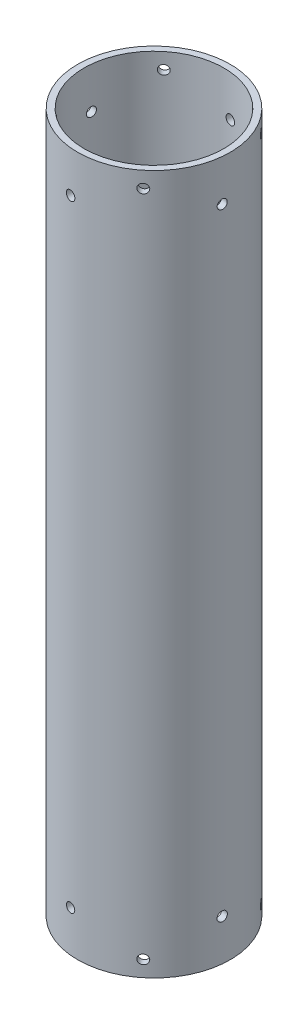
SolidWorks part; units mm, degrees
material "Thornel Mat VMA"
ref_plane "前视基准面" through (0, 0, 0) normal (0, 0, 1) x (1, 0, 0)
ref_plane "上视基准面" through (0, 0, 0) normal (0, 1, 0) x (1, 0, 0)
ref_plane "右视基准面" through (0, 0, 0) normal (1, 0, 0) x (0, 0, -1)
sketch "草图1" plane through (0, 0, 0) normal (0, 1, 0) x (1, 0, 0)
  circle A0 centre (0, 0) radius 22
  circle A1 centre (0, 0) radius 24
  dimension "D1" = 48
  dimension "D2" = 44
extrude "凸台-拉伸1" add sketch "草图1" along normal blind 220
sketch "草图2" plane through (-1.9838, 0, 19.9014) normal (0.0992, 0, -0.9951) x (-0.9951, 0, -0.0992)
  circle A0 centre (0, 13) radius 1.45
  circle A1 centre (0, 13) radius 1.45 construction
  circle A2 centre (0, 207) radius 1.5
  circle A3 centre (0, 207) radius 1.5 construction
sketch "草图3" plane through (12.6697, 0, 15.4751) normal (-0.6335, 0, -0.7738) x (-0.7738, 0, 0.6335)
  circle A0 centre (0, 5) radius 1.45
  circle A1 centre (0, 5) radius 1.45 construction
  circle A2 centre (0, 215) radius 1.45
  circle A3 centre (0, 215) radius 1.45 construction
sketch "草图4" plane through (19.9014, 0, 1.9838) normal (-0.9951, 0, -0.0992) x (-0.0992, 0, 0.9951)
  circle A0 centre (0, 13) radius 1.5
  circle A1 centre (0, 13) radius 1.5 construction
  circle A2 centre (0, 207) radius 1.45
  circle A3 centre (0, 207) radius 1.45 construction
sketch "草图5" plane through (15.4751, 0, -12.6697) normal (-0.7738, 0, 0.6335) x (0.6335, 0, 0.7738)
  circle A0 centre (0, 5) radius 1.45
  circle A1 centre (0, 5) radius 1.45 construction
  circle A2 centre (0, 215) radius 1.45
  circle A3 centre (0, 215) radius 1.45 construction
extrude "切除-拉伸1" cut sketch "草图2" against normal through all and the other way through all
extrude "切除-拉伸2" cut sketch "草图3" against normal through all and the other way through all
extrude "切除-拉伸3" cut sketch "草图5" against normal through all and the other way through all
extrude "切除-拉伸4" cut sketch "草图4" against normal through all and the other way through all
